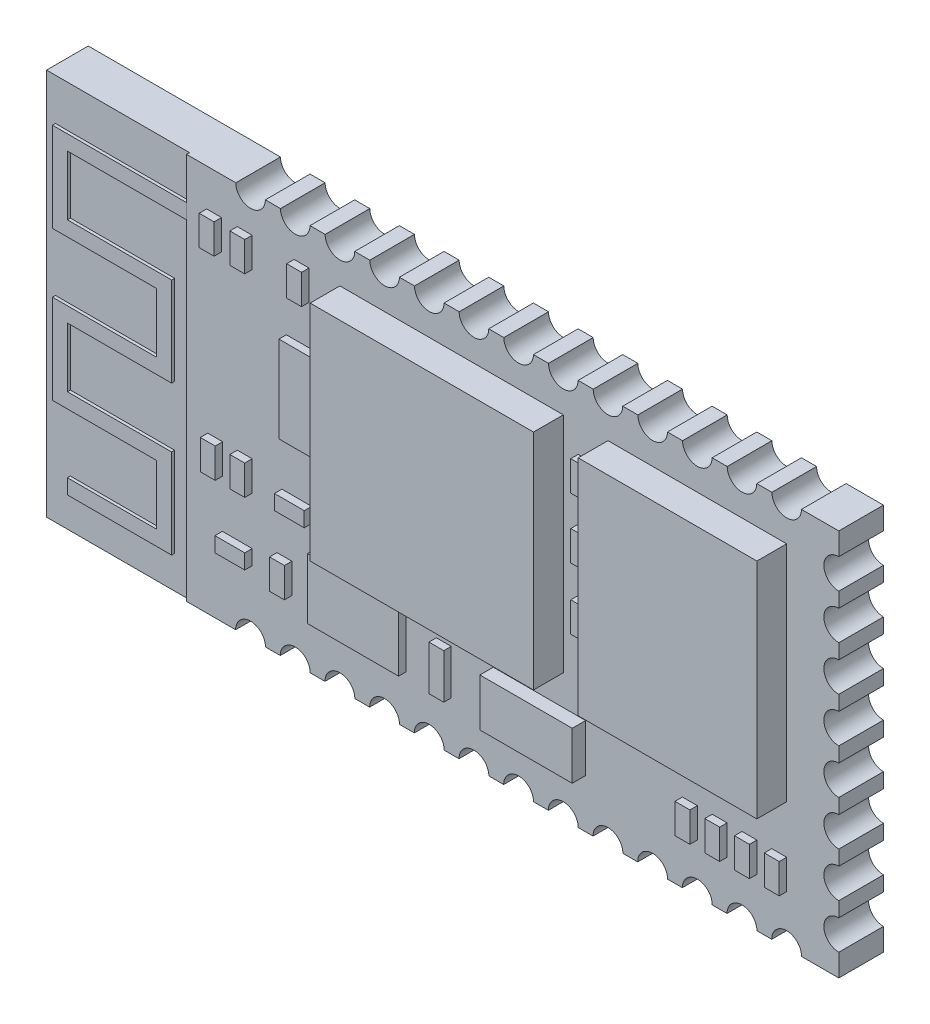
SolidWorks part; units mm, degrees
ref_plane "Front Plane" through (0, 0, 0) normal (0, 0, 1) x (1, 0, 0)
ref_plane "Top Plane" through (0, 0, 0) normal (0, 1, 0) x (1, 0, 0)
ref_plane "Right Plane" through (0, 0, 0) normal (1, 0, 0) x (0, 0, -1)
sketch "Sketch1" plane through (0, 0, 0) normal (0, 0, 1) x (1, 0, 0)
  line L1 (0, 0) -> (26.7, 0)
  line L2 (0, 0) -> (0, 13)
  line L3 (0, 13) -> (26.7, 13)
  line L4 (26.7, 0) -> (26.7, 13)
  dimension "D1" = 26.7
  dimension "D2" = 13
extrude "Boss-Extrude1" add sketch "Sketch1" along normal blind 1.5
sketch "Sketch2" plane through (0, 0, 1.5) normal (0, 0, 1) x (1, 0, 0)
  line L0 (24.4936, 13) -> (24.4936, 11.75) construction
  line L1 (26.7, 13) -> (0, 13) construction
  line L2 (26.7, 9.0019) -> (24.95, 9.0019) construction
  line L3 (26.7, 0) -> (26.7, 13) construction
  line L4 (24.95, 9.0019) -> (24.95, 13) construction
  line L5 (24.4936, 11.75) -> (26.7, 11.75) construction
  line L7 (24.95, 11.75) -> (18.95, 11.75)
  line L8 (24.95, 11.75) -> (24.95, 4.25)
  line L9 (24.95, 4.25) -> (18.95, 4.25)
  line L10 (18.95, 11.75) -> (18.95, 4.25)
  point P8 (24.95, 11.75)
  dimension "D1" = 1.25
  dimension "D2" = 1.75
  dimension "D3" = 7.5
  dimension "D4" = 6
extrude "Boss-Extrude2" add sketch "Sketch2" along normal blind 1
sketch "Sketch3" plane through (0, 0, 1.5) normal (0, 0, 1) x (1, 0, 0)
  line L0 (18.95, 11.75) -> (17.45, 11.75) construction
  line L2 (17.45, 11.75) -> (9.95, 11.75)
  line L3 (17.45, 11.75) -> (17.45, 4.25)
  line L4 (17.45, 4.25) -> (9.95, 4.25)
  line L5 (9.95, 11.75) -> (9.95, 4.25)
  dimension "D1" = 1.5
  dimension "D2" = 7.5
extrude "Boss-Extrude3" add sketch "Sketch3" along normal blind 1
sketch "Sketch4" plane through (0, 0, 1.5) normal (0, 0, 1) x (1, 0, 0)
  line L0 (26.7, 13) -> (0, 13) construction
  line L1 (0, 0) -> (4.8, 0)
  line L2 (0, 0) -> (0, 13)
  line L3 (0, 13) -> (4.8, 13)
  line L4 (4.8, 0) -> (4.8, 13)
  dimension "D1" = 4.8
extrude "Cut-Extrude1" cut sketch "Sketch4" against normal blind 0.1
sketch "Sketch5" plane through (0, 0, 1.5) normal (0, 0, 1) x (1, 0, 0)
  line L0 (26.7, 1.6369) -> (18.5825, 1.6369) construction
  line L1 (26.7, 0) -> (26.7, 13) construction
  line L2 (24.45, 2.1369) -> (23.95, 2.1369) construction
  line L3 (24.95, 1.6369) -> (24.45, 1.6369)
  line L4 (24.95, 1.6369) -> (24.95, 2.6369)
  line L5 (24.95, 2.6369) -> (24.45, 2.6369)
  line L6 (24.45, 1.6369) -> (24.45, 2.6369)
  line L11 (23.45, 2.1369) -> (22.95, 2.1369) construction
  line L12 (23.95, 1.6369) -> (23.45, 1.6369)
  line L13 (23.95, 1.6369) -> (23.95, 2.6369)
  line L14 (23.95, 2.6369) -> (23.45, 2.6369)
  line L15 (23.45, 1.6369) -> (23.45, 2.6369)
  line L16 (22.45, 2.1369) -> (21.95, 2.1369) construction
  line L17 (22.95, 1.6369) -> (22.45, 1.6369)
  line L18 (22.95, 1.6369) -> (22.95, 2.6369)
  line L19 (22.95, 2.6369) -> (22.45, 2.6369)
  line L20 (22.45, 1.6369) -> (22.45, 2.6369)
  line L21 (17.45, 4.25) -> (18.95, 4.25) construction
  line L22 (21.95, 1.6369) -> (21.45, 1.6369)
  line L23 (21.95, 1.6369) -> (21.95, 2.6369)
  line L24 (21.95, 2.6369) -> (21.45, 2.6369)
  line L25 (21.45, 1.6369) -> (21.45, 2.6369)
  line L26 (18.95, 4.25) -> (18.2, 0) construction
  line L27 (4.8, 0) -> (26.7, 0) construction
  line L28 (18.2, 0) -> (18.2, 13) construction
  line L29 (26.7, 13) -> (4.8, 13) construction
  line L31 (18.45, 10.85) -> (17.95, 10.85)
  line L32 (18.45, 10.85) -> (18.45, 9.85)
  line L33 (18.45, 9.85) -> (17.95, 9.85)
  line L34 (17.95, 10.85) -> (17.95, 9.85)
  line L35 (18.45, 10.85) -> (17.95, 9.85) construction
  line L36 (18.45, 9.85) -> (17.95, 10.85) construction
  line L37 (18.45, 8.8185) -> (17.95, 8.8185)
  line L38 (18.45, 8.8185) -> (18.45, 7.8185)
  line L39 (18.45, 7.8185) -> (17.95, 7.8185)
  line L40 (17.95, 8.8185) -> (17.95, 7.8185)
  line L41 (18.45, 8.8185) -> (17.95, 7.8185) construction
  line L42 (18.45, 7.8185) -> (17.95, 8.8185) construction
  line L43 (18.45, 6.7474) -> (17.95, 6.7474)
  line L44 (18.45, 6.7474) -> (18.45, 5.7474)
  line L45 (18.45, 5.7474) -> (17.95, 5.7474)
  line L46 (17.95, 6.7474) -> (17.95, 5.7474)
  line L47 (18.45, 6.7474) -> (17.95, 5.7474) construction
  line L48 (18.45, 5.7474) -> (17.95, 6.7474) construction
  point P36 (18.2, 10.35)
  point P41 (18.2, 8.3185)
  point P46 (18.2, 6.2474)
  dimension "D1" = 1
  dimension "D2" = 0.5
  dimension "D3" = 0.5
  dimension "D4" = 0.5
  dimension "D5" = 0.5
  dimension "D6" = 0.5
  dimension "D7" = 1
  dimension "D8" = 1
  dimension "D9" = 1
extrude "Boss-Extrude4" add sketch "Sketch5" along normal blind 0.25
sketch "Sketch6" plane through (0, 0, 1.5) normal (0, 0, 1) x (1, 0, 0)
  line L0 (18.2, 5.7474) -> (18.2, 0) construction
  line L1 (17.95, 5.7474) -> (18.45, 5.7474) construction
  line L2 (4.8, 0) -> (26.7, 0) construction
  line L3 (21.45, 1.6369) -> (4.8, 1.6369) construction
  line L4 (4.8, 0) -> (4.8, 13) construction
  line L6 (18.2, 1.6369) -> (15.1, 1.6369)
  line L7 (18.2, 1.6369) -> (18.2, 3.2369)
  line L8 (18.2, 3.2369) -> (15.1, 3.2369)
  line L9 (15.1, 1.6369) -> (15.1, 3.2369)
  dimension "D1" = 3.1
  dimension "D2" = 1.6
extrude "Boss-Extrude5" add sketch "Sketch6" along normal blind 0.45
sketch "Sketch7" plane through (0, 0, 1.5) normal (0, 0, 1) x (1, 0, 0)
  line L0 (15.1, 1.6369) -> (4.8, 1.6369) construction
  line L1 (4.8, 0) -> (4.8, 13) construction
  line L3 (12.1713, 1.6369) -> (9.1123, 1.6369)
  line L4 (12.1713, 1.6369) -> (12.1713, 3.6726)
  line L5 (12.1713, 3.6726) -> (9.1123, 3.6726)
  line L6 (9.1123, 1.6369) -> (9.1123, 3.6726)
extrude "Boss-Extrude6" add sketch "Sketch7" along normal blind 0.25
sketch "Sketch8" plane through (0, 0, 1.5) normal (0, 0, 1) x (1, 0, 0)
  line L1 (13.1877, 1.6369) -> (13.6877, 1.6369)
  line L2 (13.1877, 1.6369) -> (13.1877, 3.1369)
  line L3 (13.1877, 3.1369) -> (13.6877, 3.1369)
  line L4 (13.6877, 1.6369) -> (13.6877, 3.1369)
  dimension "D1" = 0.5
  dimension "D2" = 1.5
extrude "Boss-Extrude7" add sketch "Sketch8" along normal blind 0.25
sketch "Sketch9" plane through (0, 0, 1.5) normal (0, 0, 1) x (1, 0, 0)
  line L0 (9.95, 11.75) -> (4.8, 11.75) construction
  line L1 (4.8, 0) -> (4.8, 13) construction
  line L3 (8.9117, 11.75) -> (8.4117, 11.75)
  line L4 (8.9117, 11.75) -> (8.9117, 10.75)
  line L5 (8.9117, 10.75) -> (8.4117, 10.75)
  line L6 (8.4117, 11.75) -> (8.4117, 10.75)
  line L7 (5.4755, 11.75) -> (5.9755, 11.75)
  line L8 (5.4755, 11.75) -> (5.4755, 10.75)
  line L9 (5.4755, 10.75) -> (5.9755, 10.75)
  line L10 (5.9755, 11.75) -> (5.9755, 10.75)
  line L11 (6.5043, 11.75) -> (7.0043, 11.75)
  line L12 (6.5043, 11.75) -> (6.5043, 10.75)
  line L13 (6.5043, 10.75) -> (7.0043, 10.75)
  line L14 (7.0043, 11.75) -> (7.0043, 10.75)
  dimension "D1" = 0.5
  dimension "D2" = 1
  dimension "D3" = 0.5
  dimension "D4" = 1
  dimension "D5" = 1
  dimension "D6" = 0.5
extrude "Boss-Extrude8" add sketch "Sketch9" along normal blind 0.25
sketch "Sketch10" plane through (0, 0, 1.5) normal (0, 0, 1) x (1, 0, 0)
  line L1 (8.1526, 6.5266) -> (9.4588, 6.5266)
  line L2 (8.1526, 6.5266) -> (8.1526, 9.4292)
  line L3 (8.1526, 9.4292) -> (9.4588, 9.4292)
  line L4 (9.4588, 6.5266) -> (9.4588, 9.4292)
extrude "Boss-Extrude9" add sketch "Sketch10" along normal blind 0.25
sketch "Sketch11" plane through (0, 0, 1.5) normal (0, 0, 1) x (1, 0, 0)
  line L0 (7.0043, 10.75) -> (7.0043, 0) construction
  line L1 (4.8, 0) -> (26.7, 0) construction
  line L3 (7.0043, 4.25) -> (6.5043, 4.25)
  line L4 (7.0043, 4.25) -> (7.0043, 5.25)
  line L5 (7.0043, 5.25) -> (6.5043, 5.25)
  line L6 (6.5043, 4.25) -> (6.5043, 5.25)
  line L7 (6.0131, 4.25) -> (5.5131, 4.25)
  line L8 (6.0131, 4.25) -> (6.0131, 5.25)
  line L9 (6.0131, 5.25) -> (5.5131, 5.25)
  line L10 (5.5131, 4.25) -> (5.5131, 5.25)
  line L11 (8.0025, 4.366) -> (9.0025, 4.366)
  line L12 (8.0025, 4.366) -> (8.0025, 4.866)
  line L13 (8.0025, 4.866) -> (9.0025, 4.866)
  line L14 (9.0025, 4.366) -> (9.0025, 4.866)
  line L15 (7.8366, 1.938) -> (8.3366, 1.938)
  line L16 (7.8366, 1.938) -> (7.8366, 2.938)
  line L17 (7.8366, 2.938) -> (8.3366, 2.938)
  line L18 (8.3366, 1.938) -> (8.3366, 2.938)
  line L19 (6.0043, 2.1395) -> (7.0043, 2.1395)
  line L20 (6.0043, 2.1395) -> (6.0043, 2.6395)
  line L21 (6.0043, 2.6395) -> (7.0043, 2.6395)
  line L22 (7.0043, 2.1395) -> (7.0043, 2.6395)
  dimension "D1" = 0.5
  dimension "D2" = 0.5
  dimension "D3" = 1
  dimension "D4" = 1
  dimension "D5" = 1
  dimension "D6" = 0.5
  dimension "D7" = 1
  dimension "D8" = 0.5
  dimension "D9" = 1
  dimension "D10" = 0.5
extrude "Boss-Extrude10" add sketch "Sketch11" along normal blind 0.25
sketch "Sketch12" plane through (0, 0, 1.5) normal (0, 0, 1) x (1, 0, 0)
  line L0 (26.7, 0) -> (26.7, 1.25) construction
  line L1 (26.7, 0) -> (26.7, 13) construction
  line L2 (26.7, 1.25) -> (26.2, 1.25) construction
  line L3 (26.7, 0.7493) -> (26.7, 1.7507)
  line L4 (26.7, 2.2493) -> (26.7, 3.2507)
  line L5 (26.7, 3.7493) -> (26.7, 4.7507)
  line L6 (26.7, 5.2493) -> (26.7, 6.2507)
  line L7 (26.7, 6.7493) -> (26.7, 7.7507)
  line L8 (26.7, 8.2493) -> (26.7, 9.2507)
  line L9 (26.7, 9.7493) -> (26.7, 10.7507)
  line L10 (26.7, 11.2493) -> (26.7, 12.2507)
  arc A0 (26.7, 1.7507) -> (26.7, 0.7493) centre (26.7, 1.25) ccw
  arc A1 (26.7, 3.2507) -> (26.7, 2.2493) centre (26.7, 2.75) ccw
  arc A2 (26.7, 4.7507) -> (26.7, 3.7493) centre (26.7, 4.25) ccw
  arc A3 (26.7, 6.2507) -> (26.7, 5.2493) centre (26.7, 5.75) ccw
  arc A4 (26.7, 7.7507) -> (26.7, 6.7493) centre (26.7, 7.25) ccw
  arc A5 (26.7, 9.2507) -> (26.7, 8.2493) centre (26.7, 8.75) ccw
  arc A6 (26.7, 10.7507) -> (26.7, 9.7493) centre (26.7, 10.25) ccw
  arc A7 (26.7, 12.2507) -> (26.7, 11.2493) centre (26.7, 11.75) ccw
  dimension "D1" = 1.25
  dimension "D2" = 0.5
  dimension "D3" = 8
extrude "Cut-Extrude2" cut sketch "Sketch12" against normal through all
sketch "Sketch13" plane through (0, 0, 1.5) normal (0, 0, 1) x (1, 0, 0)
  line L0 (26.7, 13) -> (24.95, 13) construction
  line L1 (26.7, 13) -> (4.8, 13) construction
  line L2 (24.95, 13) -> (24.95, 12.5) construction
  line L3 (25.4463, 13) -> (24.4537, 13)
  line L4 (23.9463, 13) -> (22.9537, 13)
  line L5 (22.4463, 13) -> (21.4537, 13)
  line L6 (20.9463, 13) -> (19.9537, 13)
  line L7 (19.4463, 13) -> (18.4537, 13)
  line L8 (17.9463, 13) -> (16.9537, 13)
  line L9 (16.4463, 13) -> (15.4537, 13)
  line L10 (14.9463, 13) -> (13.9537, 13)
  line L11 (13.4463, 13) -> (12.4537, 13)
  line L12 (11.9463, 13) -> (10.9537, 13)
  line L13 (10.4463, 13) -> (9.4537, 13)
  line L14 (8.9463, 13) -> (7.9537, 13)
  line L15 (7.4463, 13) -> (6.4537, 13)
  arc A0 (24.4537, 13) -> (25.4463, 13) centre (24.95, 13) ccw
  arc A1 (22.9537, 13) -> (23.9463, 13) centre (23.45, 13) ccw
  arc A2 (21.4537, 13) -> (22.4463, 13) centre (21.95, 13) ccw
  arc A3 (19.9537, 13) -> (20.9463, 13) centre (20.45, 13) ccw
  arc A4 (18.4537, 13) -> (19.4463, 13) centre (18.95, 13) ccw
  arc A5 (16.9537, 13) -> (17.9463, 13) centre (17.45, 13) ccw
  arc A6 (15.4537, 13) -> (16.4463, 13) centre (15.95, 13) ccw
  arc A7 (13.9537, 13) -> (14.9463, 13) centre (14.45, 13) ccw
  arc A8 (12.4537, 13) -> (13.4463, 13) centre (12.95, 13) ccw
  arc A9 (10.9537, 13) -> (11.9463, 13) centre (11.45, 13) ccw
  arc A10 (9.4537, 13) -> (10.4463, 13) centre (9.95, 13) ccw
  arc A11 (7.9537, 13) -> (8.9463, 13) centre (8.45, 13) ccw
  arc A12 (6.4537, 13) -> (7.4463, 13) centre (6.95, 13) ccw
  dimension "D1" = 1.75
  dimension "D2" = 0.5
  dimension "D3" = 13
extrude "Cut-Extrude3" cut sketch "Sketch13" against normal through all contours L3 A0 | L5 A2 | L6 A3 | L7 A4 | L8 A5 | L9 A6 | L4 A1 | L11 A8 | L12 A9 | L10 A7 | L13 A10 | L14 A11 | L15 A12
sketch "Sketch15" plane through (0, 0, 1.5) normal (0, 0, 1) x (1, 0, 0)
  line L0 (26.7, 0) -> (24.95, 0) construction
  line L1 (4.8, 0) -> (26.7, 0) construction
  line L2 (24.95, 0) -> (24.95, 0.5) construction
  line L3 (24.4486, 0) -> (25.4514, 0)
  line L4 (22.9486, 0) -> (23.9514, 0)
  line L5 (21.4486, 0) -> (22.4514, 0)
  line L6 (19.9486, 0) -> (20.9514, 0)
  line L7 (18.4486, 0) -> (19.4514, 0)
  line L8 (16.9486, 0) -> (17.9514, 0)
  line L9 (15.4486, 0) -> (16.4514, 0)
  line L10 (13.9486, 0) -> (14.9514, 0)
  line L11 (12.4486, 0) -> (13.4514, 0)
  line L12 (10.9486, 0) -> (11.9514, 0)
  line L13 (9.4486, 0) -> (10.4514, 0)
  line L14 (7.9486, 0) -> (8.9514, 0)
  line L15 (6.4486, 0) -> (7.4514, 0)
  arc A0 (24.4486, 0) -> (25.4514, 0) centre (24.95, 0) cw
  arc A1 (22.9486, 0) -> (23.9514, 0) centre (23.45, 0) cw
  arc A2 (21.4486, 0) -> (22.4514, 0) centre (21.95, 0) cw
  arc A3 (19.9486, 0) -> (20.9514, 0) centre (20.45, 0) cw
  arc A4 (18.4486, 0) -> (19.4514, 0) centre (18.95, 0) cw
  arc A5 (16.9486, 0) -> (17.9514, 0) centre (17.45, 0) cw
  arc A6 (15.4486, 0) -> (16.4514, 0) centre (15.95, 0) cw
  arc A7 (13.9486, 0) -> (14.9514, 0) centre (14.45, 0) cw
  arc A8 (12.4486, 0) -> (13.4514, 0) centre (12.95, 0) cw
  arc A9 (10.9486, 0) -> (11.9514, 0) centre (11.45, 0) cw
  arc A10 (9.4486, 0) -> (10.4514, 0) centre (9.95, 0) cw
  arc A11 (7.9486, 0) -> (8.9514, 0) centre (8.45, 0) cw
  arc A12 (6.4486, 0) -> (7.4514, 0) centre (6.95, 0) cw
  dimension "D1" = 13
extrude "Cut-Extrude4" cut sketch "Sketch15" against normal through all contours L3 A0 | L4 A1 | L5 A2 | L6 A3 | L7 A4 | L9 A6 | L8 A5 | L10 A7 | L12 A9 | L11 A8 | L14 A11 | L13 A10 | L15 A12
sketch "Sketch17" plane through (0, 0, 1.4) normal (0, 0, 1) x (1, 0, 0)
  line L0 (4.8, 11.5969) -> (0.3, 11.5969)
  line L1 (4.8, 0) -> (4.8, 13) construction
  line L2 (0.3, 11.5969) -> (0.3, 8.5969)
  line L3 (0.3, 8.5969) -> (3.8, 8.5969)
  line L4 (4.8, 11.5969) -> (4.8, 11.0965)
  line L5 (4.8, 0) -> (4.8, 13) construction
  line L6 (4.8, 11.0965) -> (0.8, 11.0965)
  line L7 (0.8, 11.0965) -> (0.8, 9.0965)
  line L8 (0.8, 9.0965) -> (4.3, 9.0965)
  line L9 (4.3, 9.0965) -> (4.3, 6.0965)
  line L10 (4.3, 6.0965) -> (0.8, 6.0965)
  line L11 (0.8, 6.0965) -> (0.8, 4.0965)
  line L12 (0.8, 4.0965) -> (4.3, 4.0965)
  line L13 (4.3, 4.0965) -> (4.3, 1.0965)
  line L14 (4.3, 1.0965) -> (0.8, 1.0965)
  line L15 (0.8, 1.0965) -> (0.8, 1.5965)
  line L16 (0.8, 1.5965) -> (3.8, 1.5965)
  line L17 (3.8, 1.5965) -> (3.8, 3.5965)
  line L18 (3.8, 3.5965) -> (0.3, 3.5965)
  line L19 (0.3, 3.5965) -> (0.3, 6.5965)
  line L20 (0.3, 6.5965) -> (3.8, 6.5965)
  line L21 (3.8, 6.5965) -> (3.8, 8.5969)
  dimension "D1" = 4.5
  dimension "D2" = 3
  dimension "D3" = 3.5
  dimension "D4" = 0.5003
  dimension "D5" = 4
  dimension "D6" = 2
  dimension "D7" = 3.5
extrude "Boss-Extrude11" add sketch "Sketch17" along normal blind 0.1 separate body
